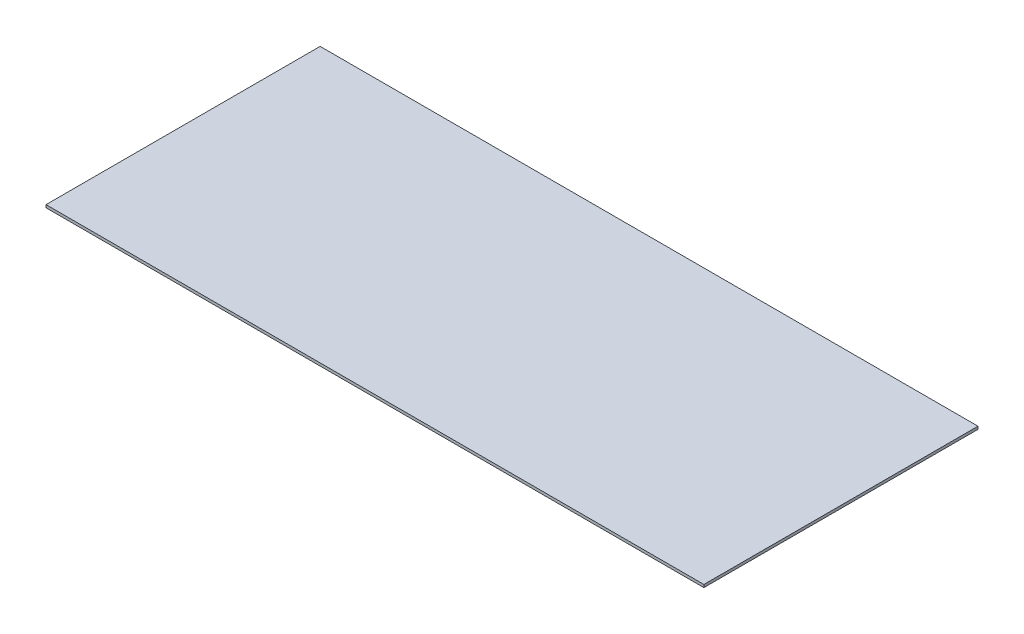
SolidWorks part; units mm, degrees
ref_plane "Plan de face" through (0, 0, 0) normal (0, 0, 1) x (1, 0, 0)
ref_plane "Plan de dessus" through (0, 0, 0) normal (0, 1, 0) x (1, 0, 0)
ref_plane "Plan de droite" through (0, 0, 0) normal (1, 0, 0) x (0, 0, -1)
sketch "Esquisse1" plane through (0, 0, 0) normal (0, 0, 1) x (1, 0, 0)
  line L0 (600, 0) -> (-600, 0)
  line L1 (-600, 0) -> (-600, 5)
  line L2 (-600, 5) -> (600, 5)
  line L3 (600, 5) -> (600, 0)
  point P3 (195.0487, 126.7863)
  point P6 (0, 0)
  dimension "D1" = 5
  dimension "D2" = 1200
extrude "Boss.-Extru.1" add sketch "Esquisse1" along normal blind 500 contours L0 L1 L2 L3
